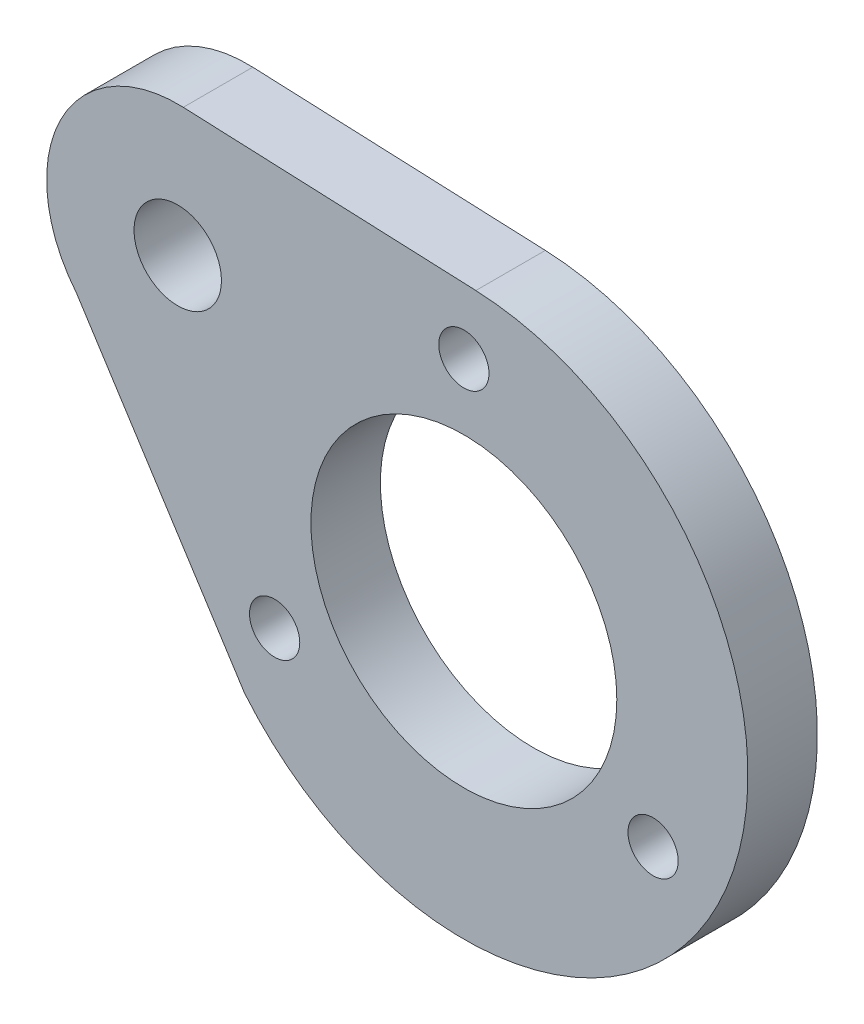
SolidWorks part; units mm, degrees
ref_plane "Front Plane" through (0, 0, 0) normal (0, 0, 1) x (1, 0, 0)
ref_plane "Top Plane" through (0, 0, 0) normal (0, 1, 0) x (1, 0, 0)
ref_plane "Right Plane" through (0, 0, 0) normal (1, 0, 0) x (0, 0, -1)
sketch "Sketch1" plane through (0, 0, 0) normal (0, 0, 1) x (1, 0, 0)
  line L0 (45.355, 50.7945) -> (45.355, 55.7945) construction
  line L1 (38.8078, 54.5745) -> (45.355, 50.7945) construction
  line L2 (38.9346, 57.5719) -> (45.6296, 57.2887)
  line L3 (36.4897, 52.6702) -> (40.3324, 46.6686)
  circle A0 centre (45.355, 50.7945) radius 3.5
  circle A1 centre (45.355, 50.7945) radius 5 construction
  circle A2 centre (45.355, 55.7945) radius 0.575
  circle A3 centre (49.6851, 48.2945) radius 0.575
  circle A4 centre (41.0249, 48.2945) radius 0.575
  circle A5 centre (38.8078, 54.5745) radius 1
  circle A6 centre (38.8078, 54.5745) radius 1 construction
  arc A7 (40.3324, 46.6686) -> (45.6296, 57.2887) centre (45.355, 50.7945) ccw
  arc A8 (38.9346, 57.5719) -> (36.4897, 52.6702) centre (38.8078, 54.5745) ccw
  point P15 (45.355, 50.7945)
  dimension "D2" = 3
  dimension "D3" = 60
  dimension "D4" = 6
  dimension "D5" = 13
  dimension "D1" = 7.56
extrude "Boss-Extrude1" add sketch "Sketch1" along normal blind 1.59
